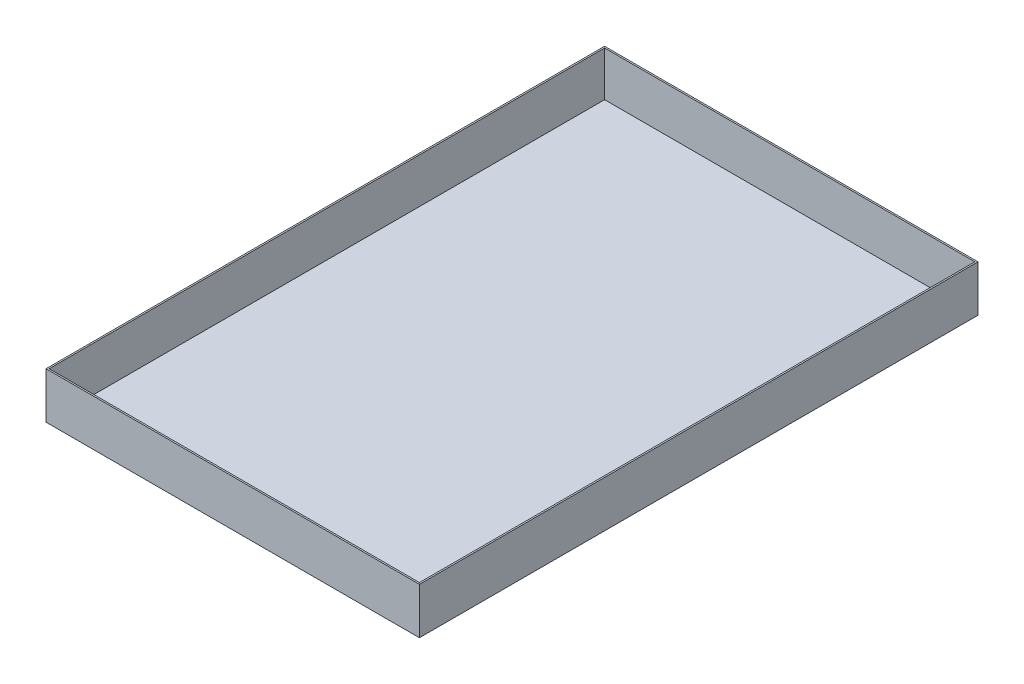
SolidWorks part; units mm, degrees
ref_plane "Front Plane" through (0, 0, 0) normal (0, 0, 1) x (1, 0, 0)
ref_plane "Top Plane" through (0, 0, 0) normal (0, 1, 0) x (1, 0, 0)
ref_plane "Right Plane" through (0, 0, 0) normal (1, 0, 0) x (0, 0, -1)
sketch "Sketch1" plane through (0, 0, 0) normal (0, 1, 0) x (1, 0, 0)
  line L1 (0, 0) -> (614.68, 0)
  line L2 (0, 0) -> (0, 919.48)
  line L3 (0, 919.48) -> (614.68, 919.48)
  line L4 (614.68, 0) -> (614.68, 919.48)
  dimension "D1" = 919.48
  dimension "D2" = 614.68
extrude "Boss-Extrude1" add sketch "Sketch1" along normal blind 76.2
shell "Shell1" thickness 2.54
